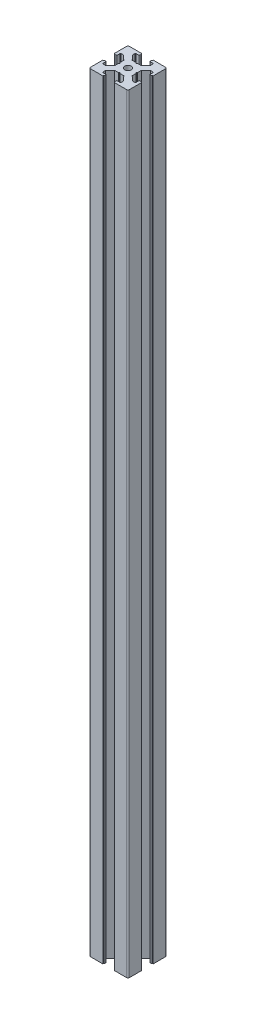
SolidWorks part; units mm, degrees
ref_plane "Front Plane" through (0, 0, 0) normal (0, 0, 1) x (1, 0, 0)
ref_plane "Top Plane" through (0, 0, 0) normal (0, 1, 0) x (1, 0, 0)
ref_plane "Right Plane" through (0, 0, 0) normal (1, 0, 0) x (0, 0, -1)
sketch "Sketch3" plane through (0, 0, 0) normal (0, 1, 0) x (1, 0, 0)
  line L0 (11, 30) -> (11, 27.75)
  line L1 (0, 0) -> (30, 0)
  line L2 (0, 0) -> (0, 30)
  line L3 (0, 30) -> (30, 30)
  line L4 (30, 0) -> (30, 30)
  line L5 (11, 27.75) -> (8, 27.75)
  line L6 (8, 27.75) -> (8, 25.5)
  line L7 (8, 25.5) -> (11.5, 21.75)
  line L8 (11.5, 21.75) -> (18.5, 21.75)
  line L9 (18.5, 21.75) -> (22, 25.5)
  line L10 (22, 25.5) -> (22, 27.75)
  line L11 (22, 27.75) -> (19, 27.75)
  line L12 (19, 27.75) -> (19, 30)
  line L13 (19, 30) -> (11, 30)
  line L14 (14.5, 21.75) -> (15, 21.25)
  line L15 (15, 21.25) -> (15.5, 21.75)
  line L16 (15.5, 21.75) -> (14.5, 21.75)
  line L17 (19, 29.5) -> (19, 30)
  line L18 (19.5, 30) -> (19, 30)
  line L19 (11, 29.5) -> (11, 30)
  line L20 (10.5, 30) -> (11, 30)
  line L21 (0, 19) -> (2.25, 19)
  line L22 (2.25, 19) -> (2.25, 22)
  line L23 (2.25, 22) -> (4.5, 22)
  line L24 (4.5, 22) -> (8.25, 18.5)
  line L25 (8.25, 18.5) -> (8.25, 11.5)
  line L26 (8.25, 11.5) -> (4.5, 8)
  line L27 (4.5, 8) -> (2.25, 8)
  line L28 (2.25, 8) -> (2.25, 11)
  line L29 (2.25, 11) -> (0, 11)
  line L30 (0, 11) -> (0, 19)
  line L31 (8.25, 15.5) -> (8.25, 14.5)
  line L32 (8.25, 14.5) -> (8.75, 15)
  line L33 (8.75, 15) -> (8.25, 15.5)
  line L34 (0.5, 19) -> (0, 19)
  line L35 (0, 19.5) -> (0, 19)
  line L36 (0, 10.5) -> (0, 11)
  line L37 (0.5, 11) -> (0, 11)
  line L38 (15, 30) -> (15, 0) construction
  line L39 (30, 15) -> (0, 15) construction
  line L40 (15, 8.75) -> (15.5, 8.25)
  line L41 (14.5, 8.25) -> (15, 8.75)
  line L42 (15.5, 8.25) -> (14.5, 8.25)
  line L43 (19.5, 0) -> (19, 0)
  line L44 (19, 0.5) -> (19, 0)
  line L45 (10.5, 0) -> (11, 0)
  line L46 (11, 0.5) -> (11, 0)
  line L47 (19, 2.25) -> (19, 0)
  line L48 (22, 2.25) -> (19, 2.25)
  line L49 (22, 4.5) -> (22, 2.25)
  line L50 (18.5, 8.25) -> (22, 4.5)
  line L51 (11.5, 8.25) -> (18.5, 8.25)
  line L52 (8, 4.5) -> (11.5, 8.25)
  line L53 (8, 2.25) -> (8, 4.5)
  line L54 (11, 2.25) -> (8, 2.25)
  line L55 (11, 0) -> (11, 2.25)
  line L56 (19, 0) -> (11, 0)
  line L57 (21.75, 14.5) -> (21.25, 15)
  line L58 (21.75, 15.5) -> (21.75, 14.5)
  line L59 (21.25, 15) -> (21.75, 15.5)
  line L60 (29.5, 11) -> (30, 11)
  line L61 (30, 10.5) -> (30, 11)
  line L62 (30, 19.5) -> (30, 19)
  line L63 (29.5, 19) -> (30, 19)
  line L64 (27.75, 11) -> (30, 11)
  line L65 (27.75, 8) -> (27.75, 11)
  line L66 (25.5, 8) -> (27.75, 8)
  line L67 (21.75, 11.5) -> (25.5, 8)
  line L68 (21.75, 18.5) -> (21.75, 11.5)
  line L69 (25.5, 22) -> (21.75, 18.5)
  line L70 (27.75, 22) -> (25.5, 22)
  line L71 (27.75, 19) -> (27.75, 22)
  line L72 (30, 19) -> (27.75, 19)
  line L73 (30, 11) -> (30, 19)
  arc A0 (19.5, 30) -> (19, 29.5) centre (19, 30) cw
  arc A1 (10.5, 30) -> (11, 29.5) centre (11, 30) ccw
  arc A2 (0.5, 19) -> (0, 19.5) centre (0, 19) ccw
  arc A3 (0.5, 11) -> (0, 10.5) centre (0, 11) cw
  arc A4 (19.5, 0) -> (19, 0.5) centre (19, 0) ccw
  arc A5 (10.5, 0) -> (11, 0.5) centre (11, 0) cw
  arc A6 (29.5, 11) -> (30, 10.5) centre (30, 11) ccw
  arc A7 (29.5, 19) -> (30, 19.5) centre (30, 19) cw
  point P7 (15, 21.75)
  point P16 (15, 30)
  point P26 (8.25, 15)
  point P35 (0, 15)
  dimension "D16" = 0.5
  dimension "D17" = 0.5
  dimension "D28" = 0.5
  dimension "D29" = 0.5
  dimension "D1" = 30
  dimension "D2" = 30
  dimension "D3" = 11
  dimension "D4" = 11
  dimension "D5" = 2.25
  dimension "D6" = 2.25
  dimension "D7" = 3
  dimension "D8" = 3
  dimension "D9" = 2.25
  dimension "D10" = 2.25
  dimension "D11" = 7
  dimension "D12" = 8.25
  dimension "D13" = 0.5
  dimension "D14" = 0.5
  dimension "D15" = 0.5
  dimension "D18" = 11
  dimension "D19" = 11
  dimension "D20" = 2.25
  dimension "D21" = 2.25
  dimension "D22" = 3
  dimension "D23" = 7
  dimension "D24" = 8.25
  dimension "D25" = 0.5
  dimension "D26" = 0.5
  dimension "D27" = 0.5
extrude "Boss-Extrude1" add sketch "Sketch3" along normal blind 594 contours L72 A7 L4 L3 A0 L12 L11 L10 L9 L8 L15 L14 L7 L6 L5 L0 A1 L2 A2 L21 L22 L23 L24 L25 L33 L32 L26 L27 L28 L29 A3 L1 A5 L55 L54 L53 L52 L51 L41 L40 L50 L49 L48 L47 A4
fillet "Fillet1" radius 1 4 edges at (0, 297, 0) (30, 297, 0) (30, 297, -30) (0, 297, -30)
sketch "Sketch4" plane through (0, 594, 0) normal (0, 1, 0) x (1, 0, 0)
  line L0 (18.5, 21.75) -> (8.25, 11.5) construction
  line L1 (21.75, 18.5) -> (11.5, 8.25) construction
  line L2 (15.5, 21.75) -> (21.75, 15.5) construction
  line L9 (8.25, 14.5) -> (14.5, 8.25) construction
  line L10 (8.25, 15.5) -> (14.5, 21.75) construction
  line L11 (21.75, 14.5) -> (15.5, 8.25) construction
  line L12 (11.5, 21.75) -> (21.75, 11.5) construction
  line L13 (8.25, 18.5) -> (18.5, 8.25) construction
  line L20 (30, 15) -> (0, 15) construction
  circle A0 centre (15, 15) radius 2.5
  dimension "D1" = 5
extrude "Cut-Extrude1" cut sketch "Sketch4" against normal through all
fillet "Fillet2" radius 0.5 24 edges at (2.25, 297, -22) (2.25, 297, -19) (8.25, 297, -15.5) (8.25, 297, -14.5) (2.25, 297, -11) (2.25, 297, -8) (8, 297, -2.25) (11, 297, -2.25) (14.5, 297, -8.25) (15.5, 297, -8.25) (19, 297, -2.25) (22, 297, -2.25) (27.75, 297, -8) (27.75, 297, -11) (27.75, 297, -19) (27.75, 297, -22) (21.75, 297, -14.5) (21.75, 297, -15.5) (15.5, 297, -21.75) (14.5, 297, -21.75) (22, 297, -27.75) (19, 297, -27.75) (11, 297, -27.75) (8, 297, -27.75)
